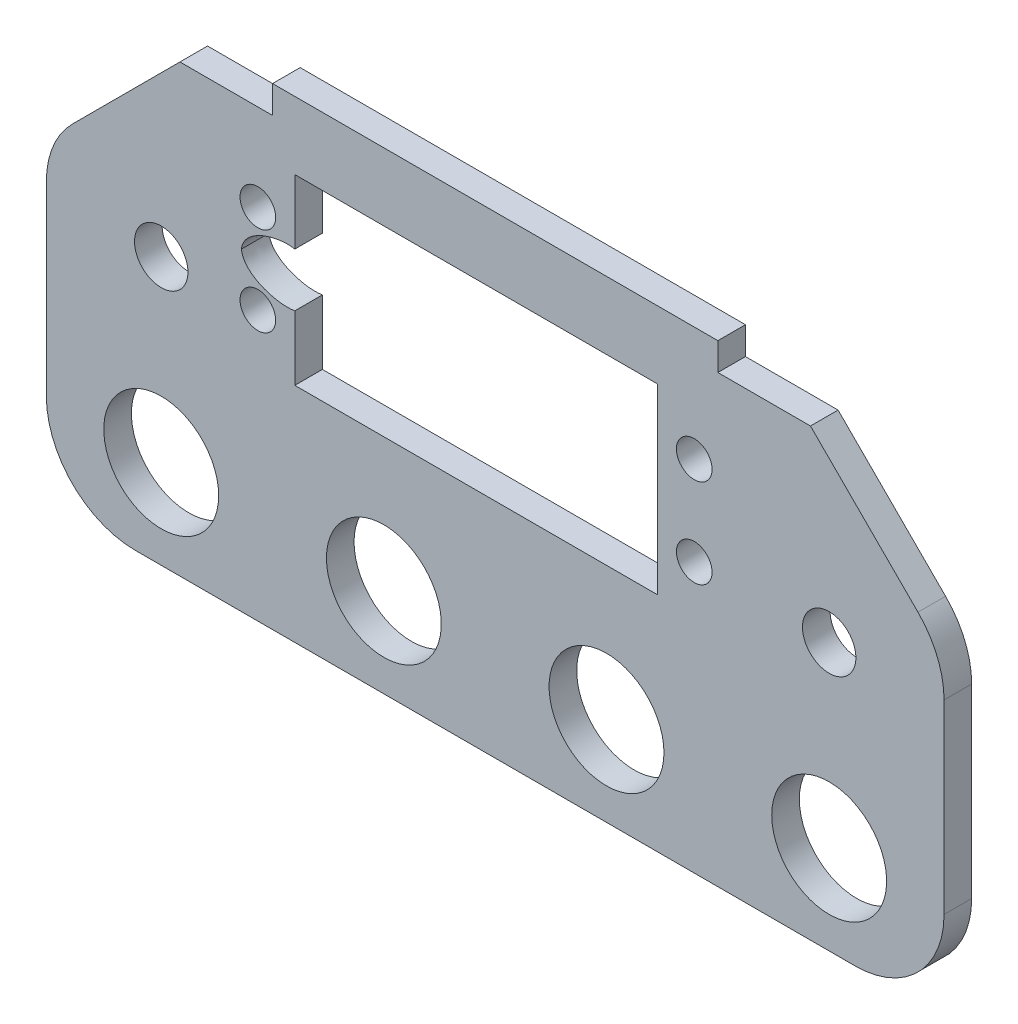
SolidWorks part; units mm, degrees
material "Teak"
ref_plane "Front Plane" through (0, 0, 0) normal (0, 0, 1) x (1, 0, 0)
ref_plane "Top Plane" through (0, 0, 0) normal (0, 1, 0) x (1, 0, 0)
ref_plane "Right Plane" through (0, 0, 0) normal (1, 0, 0) x (0, 0, -1)
sketch "Sketch4" plane through (0, 0, 0) normal (0, 0, 1) x (1, 0, 0)
  line L0 (0, 41.3027) -> (0, -5.0008) construction
  line L1 (50.4, -5.0008) -> (-50.4, -5.0008)
  line L2 (50.4, -5.0008) -> (50.4, 44.9992)
  line L3 (-0.4, 44.9992) -> (19.6, 44.9992)
  line L5 (-50.4, -5.0008) -> (-50.4, 44.9992)
  line L6 (19.6, 44.9992) -> (50.4, 44.9992)
  line L9 (-0.4, 44.9992) -> (-50.4, 44.9992)
  circle A0 centre (12.5, 5) radius 6.45
  circle A3 centre (-37.5, 4.9992) radius 6.45
  circle A5 centre (37.5, 4.9992) radius 6.45
  circle A9 centre (-12.5, 5) radius 6.45
  point P0 (0, 0)
  point P22 (0, 30)
  point P25 (0, 30)
  dimension "D4" = 12.9
  dimension "D7" = 12.9
  dimension "D12" = 10
  dimension "D8" = 25
  dimension "D5" = 12.9
  dimension "D6" = 25
  dimension "D2" = 50
  dimension "D3" = 25
  dimension "D13" = 0
  dimension "D14" = 0
  dimension "D15" = 0
extrude "Boss-Extrude3" add sketch "Sketch4" along normal blind 3.1
sketch "Sketch5" plane through (0, 0, 0) normal (0, 0, 1) x (1, 0, 0)
  line L0 (-2.15, 5.5276) -> (-2.15, 70.5276) construction
  line L1 (-2.15, 30.25) -> (-28.5, 30.25) construction
  line L2 (-2.15, 30.25) -> (64.0903, 30.25) construction
  line L3 (-22.5, 20) -> (18.2, 20)
  line L4 (-22.5, 20) -> (-22.5, 40.5) construction
  line L5 (-22.5, 40.5) -> (18.2, 40.5)
  line L6 (18.2, 20) -> (18.2, 40.5)
  line L7 (-22.5, 20) -> (18.2, 40.5) construction
  line L8 (-22.5, 40.5) -> (18.2, 20) construction
  line L9 (0, 0) -> (0, -34.6861) construction
  line L10 (-22.5, 27.25) -> (-22.5, 20)
  line L11 (-22.5, 33.25) -> (-22.5, 40.5)
  line L12 (50.4, 44.9992) -> (-50.4, 44.9992) construction
  circle A0 centre (22.35, 35.25) radius 2
  circle A1 centre (22.35, 25.25) radius 2
  circle A2 centre (-26.65, 25.25) radius 2
  circle A3 centre (-26.65, 35.25) radius 2
  circle A5 centre (-12.5, 30.25) radius 3.0561 construction
  circle A6 centre (37.5, 24.9992) radius 3
  circle A7 centre (-12.5, 5) radius 6.45 construction
  circle A8 centre (-37.5, 24.9992) radius 3
  spline S0 degree 3 poles (-28.5, 30.25) (-28.212, 27.895) (-24.313, 26.8885) (-22.5, 27.25) knots 0 0 0 0 1 1 1 1
  spline S1 degree 3 poles (-28.5, 30.25) (-28.212, 32.605) (-24.313, 33.6115) (-22.5, 33.25) knots 0 0 0 0 1 1 1 1
  point P5 (-2.15, 30.25)
  dimension "D5" = 4
  dimension "D9" = 6
  dimension "D10" = 10
  dimension "D12" = 6
  dimension "D1" = 40.7
  dimension "D2" = 20.5
  dimension "D3" = 10
  dimension "D4" = 49
  dimension "D6" = 15
  dimension "D7" = 0
  dimension "D8" = 6
  dimension "D11" = 20
  dimension "D13" = 75
extrude "Cut-Extrude4" cut sketch "Sketch5" along normal through all
fillet "Fillet1" radius 10 2 edges at (-50.4, -5.0008, 1.55) (50.4, -5.0008, 1.55)
sketch "Sketch6" plane through (0, 0, 3.1) normal (0, 0, 1) x (1, 0, 0)
  line L0 (0, 0) -> (0, 44.9992) construction
  line L1 (50.4, 44.9992) -> (-50.4, 44.9992) construction
  line L4 (-25, 48.0992) -> (25, 48.0992)
  line L5 (-25, 48.0992) -> (-25, 44.9992)
  line L6 (-25, 44.9992) -> (25, 44.9992)
  line L7 (25, 48.0992) -> (25, 44.9992)
  line L8 (-25, 48.0992) -> (25, 44.9992) construction
  line L9 (-25, 44.9992) -> (25, 48.0992) construction
  point P5 (0, 46.5492)
  dimension "D1" = 3.1
  dimension "D2" = 50
  dimension "D3" = 0
extrude "Boss-Extrude4" add sketch "Sketch6" against normal through all contours L4 L7 L6 L5
chamfer "Chamfer1" distance 15 angle 45 2 edges at (50.4, 44.9992, 1.55) (-50.4, 44.9992, 1.55)
fillet "Fillet2" radius 10 2 edges at (-50.4, 29.9992, 1.55) (50.4, 29.9992, 1.55)
equation "\"p\"= 20mm"
equation "\"m\"= 1"
equation "\"hole_diam\"= 4mm"
equation "\"len_grip_1\"= 50mm"
equation "\"len_grip_2\"= 50mm"
equation "\"thick\" = 3.1mm"
equation "\"thick2\"= 20mm"
equation "\"wrist_cont_bearing_diam\"=3in"
equation "\"wrist_cont_bearing_thick\"=5/16in"
equation "\"len_forearm\"= 300mm"
equation "\"wrist_bearing_diam\"=3in"
equation "\"len_link\"= 7cm"
equation "\"elbow_cont_bearing_diam\"=10cm"
equation "\"elbow_cont_bearing2_diam\"=7.5cm"
equation "\"small_bearing_outer\"=12.9mm"
equation "\"servo1_L\"=40.7mm"
equation "\"servo1_W\"=20.5mm"
equation "\"servo1_H\"=43.5mm"
equation "\"servo1_hL\"=49mm"
equation "\"servo1_hW\"=10mm"
equation "\"D6@Sketch5\"=15"
equation "\"D3@Sketch5\"=\"servo1_hW\""
equation "\"D2@Sketch5\"=\"servo1_W\""
equation "\"D1@Sketch5\"=\"servo1_L\""
equation "\"servo1_H2\"=27mm"
equation "\"servo2_L\"=40.5mm"
equation "\"servo2_W\"=20mm"
equation "\"servo2_hL\"=49mm"
equation "\"servo2_hW\"=10mm"
equation "\"large_bearing_inner\"=2.75in"
equation "\"large_bearing_outer\"=4.75in"
equation "\"large_bearing_thick\"=3/8in"
equation "\"large_bearing_h1\"=3.25in"
equation "\"D1@Boss-Extrude3\"=\"thick\""
equation "\"D5@Sketch4\"=\"small_bearing_outer\""
equation "\"D7@Sketch4\"=\"D5@Sketch4\""
equation "\"D4@Sketch4\"=\"D5@Sketch4\""
equation "\"D1@Sketch6\"=\"thick\""
